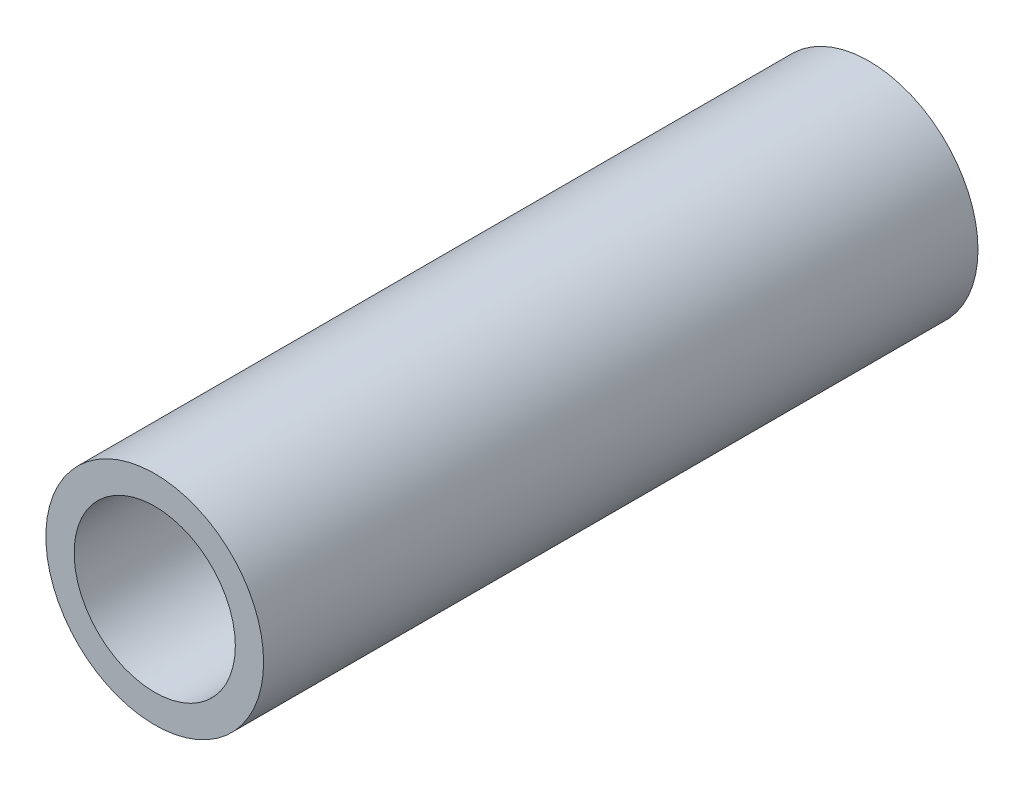
SolidWorks part; units mm, degrees
ref_plane "Front Plane" through (0, 0, 0) normal (0, 0, 1) x (1, 0, 0)
ref_plane "Top Plane" through (0, 0, 0) normal (0, 1, 0) x (1, 0, 0)
ref_plane "Right Plane" through (0, 0, 0) normal (1, 0, 0) x (0, 0, -1)
sketch "Sketch1" plane through (0, 0, 0) normal (0, 0, 1) x (1, 0, 0)
  circle A0 centre (0, 0) radius 10.668
  dimension "Pipe OD" = 21.336
extrude "Extrude-Thin1" add sketch "Sketch1" along normal mid plane 70 thin thin type one direction reverse wall 2.7686
